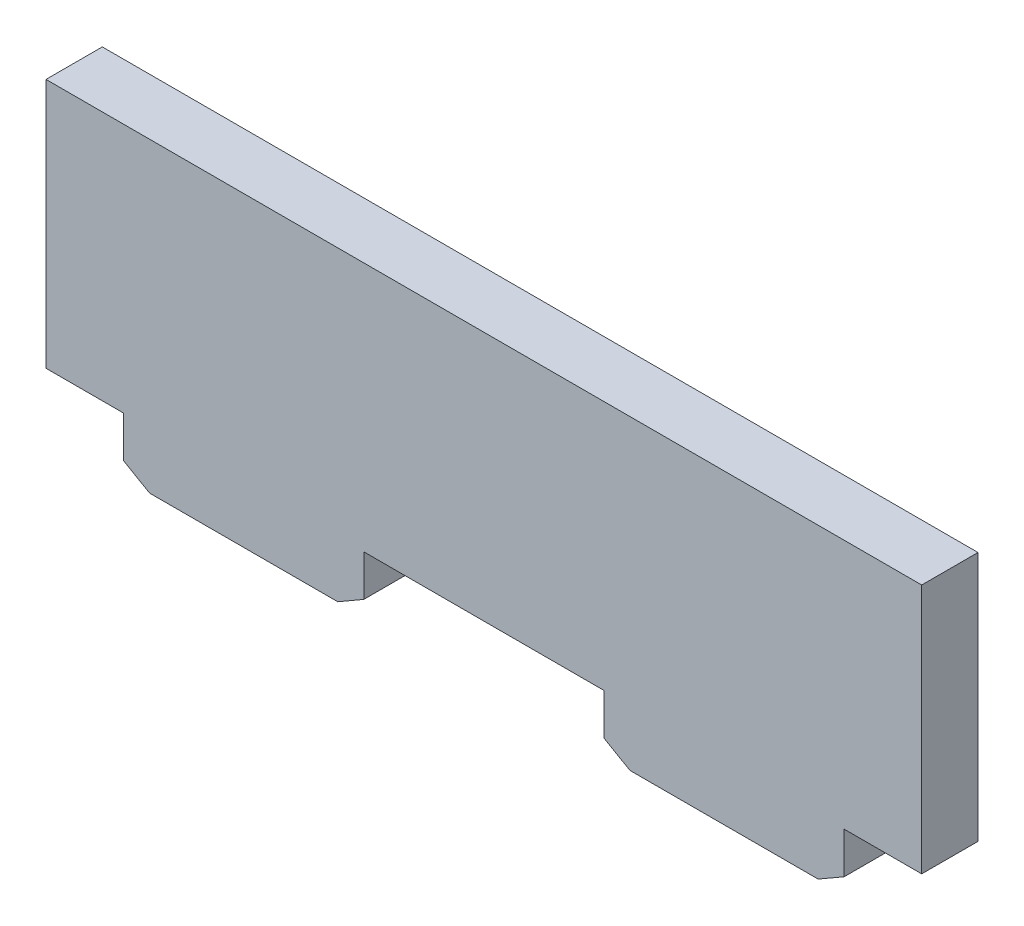
SolidWorks part; units mm, degrees
ref_plane "Front Plane" through (0, 0, 0) normal (0, 0, 1) x (1, 0, 0)
ref_plane "Top Plane" through (0, 0, 0) normal (0, 1, 0) x (1, 0, 0)
ref_plane "Right Plane" through (0, 0, 0) normal (1, 0, 0) x (0, 0, -1)
sketch "Sketch1" plane through (0, 0, 0) normal (0, 0, 1) x (1, 0, 0)
  line L1 (-22.225, 6.35) -> (22.225, 6.35)
  line L2 (-22.225, 6.35) -> (-22.225, -6.35)
  line L3 (-22.225, -6.35) -> (22.225, -6.35)
  line L4 (22.225, 6.35) -> (22.225, -6.35)
  line L5 (-22.225, 6.35) -> (22.225, -6.35) construction
  line L6 (-22.225, -6.35) -> (22.225, 6.35) construction
  point P0 (0, 0)
  dimension "D1" = 44.45
  dimension "D2" = 12.7
extrude "Boss-Extrude1" add sketch "Sketch1" along normal blind 2.8575
sketch "Sketch2" plane through (0, -6.35, 0) normal (0, -1, 0) x (-1, 0, 0)
  line L0 (0, -2.8575) -> (0, 0) construction
  line L1 (22.225, -2.8575) -> (-22.225, -2.8575) construction
  line L2 (0, 0) -> (0, -1.4287) construction
  line L3 (0, -1.4287) -> (12.192, -1.4287) construction
  line L4 (0, -1.4287) -> (-12.192, -1.4287) construction
  line L5 (22.225, 0) -> (-22.225, 0) construction
  line L6 (18.288, -2.8575) -> (6.096, -2.8575)
  line L7 (18.288, -2.8575) -> (18.288, 0)
  line L8 (18.288, 0) -> (6.096, 0)
  line L9 (6.096, -2.8575) -> (6.096, 0)
  line L10 (18.288, -2.8575) -> (6.096, 0) construction
  line L11 (18.288, 0) -> (6.096, -2.8575) construction
  line L13 (-6.096, -2.8575) -> (-18.288, -2.8575)
  line L14 (-6.096, -2.8575) -> (-6.096, 0)
  line L15 (-6.096, 0) -> (-18.288, 0)
  line L16 (-18.288, -2.8575) -> (-18.288, 0)
  line L17 (-6.096, -2.8575) -> (-18.288, 0) construction
  line L18 (-6.096, 0) -> (-18.288, -2.8575) construction
  dimension "D1" = 12.192
  dimension "D2" = 12.192
  dimension "D3" = 12.192
  dimension "D4" = 12.192
extrude "Boss-Extrude2" add sketch "Sketch2" along normal blind 2.8575
chamfer "Chamfer1" distance 0.762 angle 60 2 edges at (6.096, -9.2075, 1.4287) (-18.288, -9.2075, 1.4287)
chamfer "Chamfer2" distance 0.762 angle 60 2 edges at (18.288, -9.2075, 1.4287) (-6.096, -9.2075, 1.4287)
